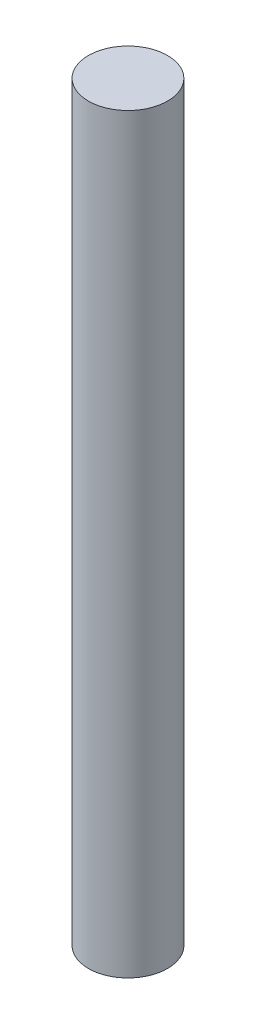
SolidWorks part; units mm, degrees
material "AISI 316 Barra de acero inoxidable recocido (SS)"
ref_plane "Alzado" through (0, 0, 0) normal (0, 0, 1) x (1, 0, 0)
ref_plane "Planta" through (0, 0, 0) normal (0, 1, 0) x (1, 0, 0)
ref_plane "Vista lateral" through (0, 0, 0) normal (1, 0, 0) x (0, 0, -1)
sketch "Croquis1" plane through (0, 0, 0) normal (0, 1, 0) x (1, 0, 0)
  circle A0 centre (0, 0) radius 20
  dimension "D1" = 40
extrude "Saliente-Extruir1" add sketch "Croquis1" along normal blind 380
